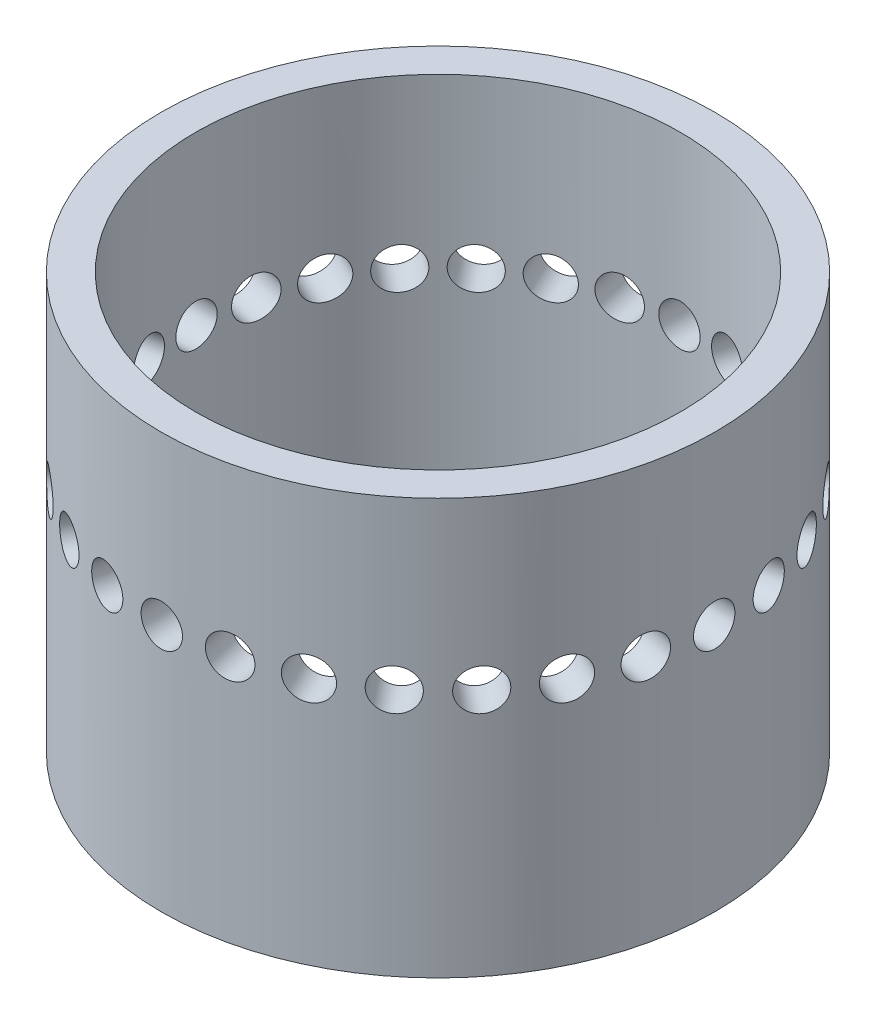
SolidWorks part; units mm, degrees
ref_plane "Front Plane" through (0, 0, 0) normal (0, 0, 1) x (1, 0, 0)
ref_plane "Top Plane" through (0, 0, 0) normal (0, 1, 0) x (1, 0, 0)
ref_plane "Right Plane" through (0, 0, 0) normal (1, 0, 0) x (0, 0, -1)
sketch "Sketch1" plane through (0, 0, 0) normal (0, 1, 0) x (1, 0, 0)
  circle A0 centre (0, 0) radius 25.4
  circle A1 centre (0, 0) radius 22.225
  dimension "D1" = 50.8
  dimension "D2" = 44.45
extrude "Boss-Extrude1" add sketch "Sketch1" along normal blind 38.1
sketch "Sketch2" plane through (0, 0, 0) normal (1, 0, 0) x (0, 0, -1)
  line L0 (0, 0) -> (0, 86.5853) construction
sketch "Sketch3" plane through (0, 0, 0) normal (1, 0, 0) x (0, 0, -1)
  line L0 (0, 0) -> (0, 86.5853) construction
  line L1 (-25.4, 0) -> (25.4, 0) construction
  circle A0 centre (0, 22.7753) radius 1.8986
  dimension "D1" = 3.7973
  dimension "D2" = 22.7753
extrude "Cut-Extrude1" cut sketch "Sketch3" against normal blind 68.326
pattern_circular "CirPattern1" count 28 over 360 about axis through (0, 0, 0) along (0, 1, 0) of "Cut-Extrude1"
